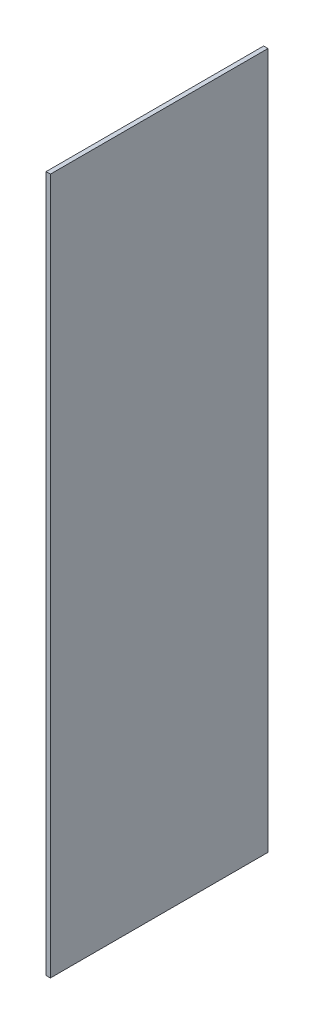
SolidWorks part; units mm, degrees
ref_plane "Front Plane" through (0, 0, 0) normal (0, 0, 1) x (1, 0, 0)
ref_plane "Top Plane" through (0, 0, 0) normal (0, 1, 0) x (1, 0, 0)
ref_plane "Right Plane" through (0, 0, 0) normal (1, 0, 0) x (0, 0, -1)
sketch "Sketch1" plane through (0, 0, 0) normal (0, 0, 1) x (1, 0, 0)
  line L1 (0, 0) -> (0.1, 0)
  line L2 (0, 0) -> (0, 16)
  line L3 (0, 16) -> (0.1, 16)
  line L4 (0.1, 0) -> (0.1, 16)
  dimension "D2" = 0.1
extrude "Boss-Extrude1" add sketch "Sketch1" along normal blind 5
equation "\"A.L\"= 0.07m"
equation "\"A.h\"= 0.007m"
equation "\"A.d\"= 0.005m"
equation "\"A.delta\"= 45.0001"
equation "\"A.w\"= 0m"
equation "\"A.v\"= 0.013m"
equation "\"A.s\"= 0.014m"
equation "\"A.t\"= 0.007m"
equation "\"B.L\"= 0.065m"
equation "\"B.h\"= 0.008m"
equation "\"B.s\"= 0.016m"
equation "\"B.t\"= 0.008m"
equation "\"C.h\"= 0.0065m"
equation "\"C.d\"= 0.005m"
equation "\"C.L\"= 0.05m"
equation "\"C.wmax\"= 0.003m"
equation "\"D.L\"= 0.06m"
equation "\"D.h\"= 0.008m"
equation "\"D.s\"= 0.012m"
equation "\"D.t\"= 0.008m"
equation "\"a_h\"= 0.0001m"
equation "\"a_d\"= 0.005m"
equation "\"a_L\"= 0.008m"
equation "\"b_h\"= 0.0004m"
equation "\"b_d\"= 0.005m"
equation "\"b_L\"= 0.008m"
equation "\"c_h\"= 0.0001m"
equation "\"c_d\"= 0.005m"
equation "\"c_L\"= 0.01m"
equation "\"d_h\"= 0.0001m"
equation "\"d_d\"= 0.005m"
equation "\"d_L\"= 0.01m"
equation "\"S.h\"= 0.015m"
equation "\"S.L\"= 0.09175m"
equation "\"D1@Sketch1\"=\"d_L\"+0.006"
equation "\"D2@Sketch1\"=\"d_h\""
equation "\"D1@Boss-Extrude1\"=\"d_d\""
